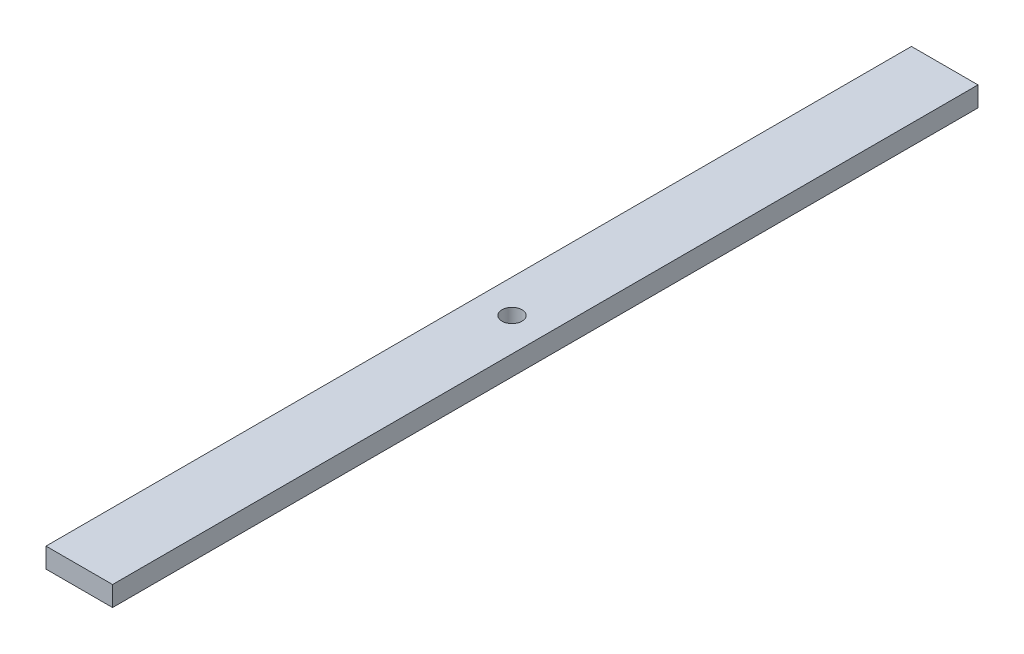
SolidWorks part; units mm, degrees
ref_plane "Front Plane" through (0, 0, 0) normal (0, 0, 1) x (1, 0, 0)
ref_plane "Top Plane" through (0, 0, 0) normal (0, 1, 0) x (1, 0, 0)
ref_plane "Right Plane" through (0, 0, 0) normal (1, 0, 0) x (0, 0, -1)
sketch "Sketch1" plane through (0, 0, 0) normal (0, 1, 0) x (1, 0, 0)
  line L1 (5, -65) -> (-5, -65)
  line L2 (5, -65) -> (5, 65)
  line L3 (5, 65) -> (-5, 65)
  line L4 (-5, -65) -> (-5, 65)
  line L5 (5, -65) -> (-5, 65) construction
  line L6 (5, 65) -> (-5, -65) construction
  circle A0 centre (0, 0) radius 1.5
  point P0 (0, 0)
  dimension "D3" = 3
  dimension "D1" = 130
  dimension "D2" = 10
extrude "Boss-Extrude1" add sketch "Sketch1" along normal blind 3
